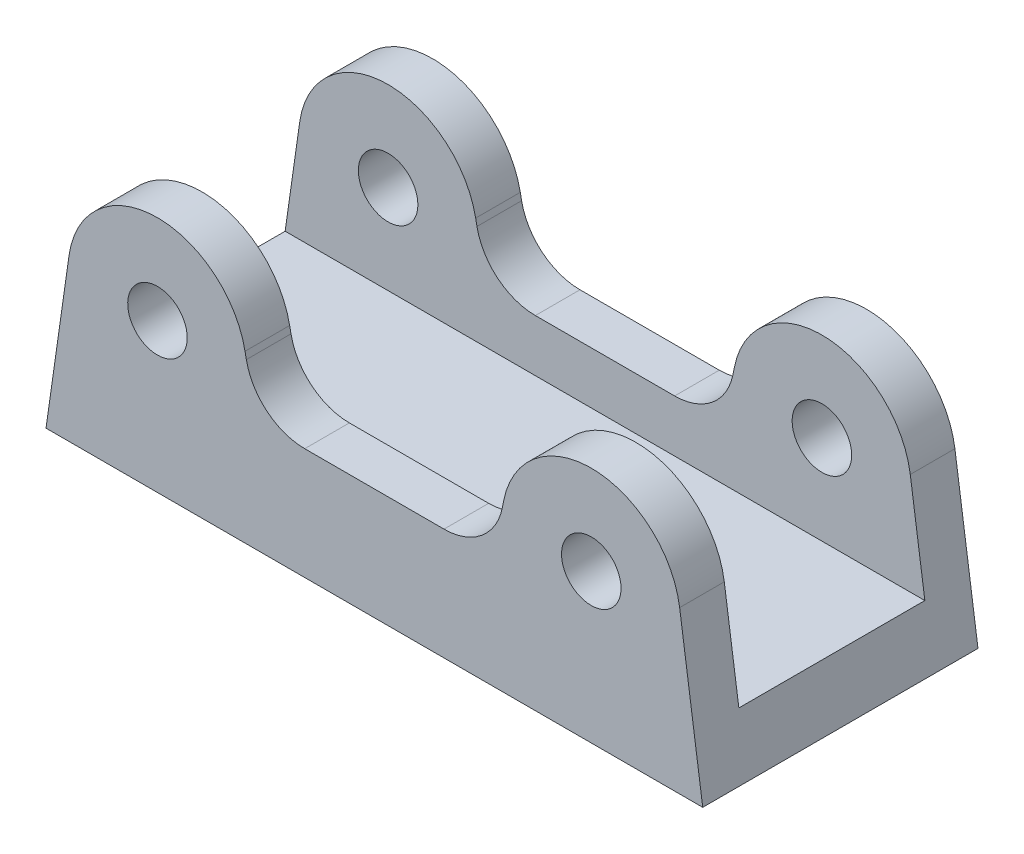
SolidWorks part; units mm, degrees
ref_plane "Front Plane" through (0, 0, 0) normal (0, 0, 1) x (1, 0, 0)
ref_plane "Top Plane" through (0, 0, 0) normal (0, 1, 0) x (1, 0, 0)
ref_plane "Right Plane" through (0, 0, 0) normal (1, 0, 0) x (0, 0, -1)
sketch "Sketch1" plane through (0, 0, 0) normal (0, 0, 1) x (1, 0, 0)
  line L0 (-29.155, 0) -> (29.155, 0) construction
  line L1 (-41.0341, 1.699) -> (-44.1376, -20)
  line L2 (-44.1376, -20) -> (44.1376, -20)
  line L3 (0, 0) -> (0, -20) construction
  line L4 (41.0341, 1.699) -> (44.1376, -20)
  line L5 (-9.3607, -5) -> (9.3607, -5)
  line L6 (-17.3837, 2.3316) -> (-17.2082, 1.4456)
  line L7 (17.3837, 2.3316) -> (17.2082, 1.4456)
  circle A0 centre (29.155, 0) radius 4
  circle A1 centre (-29.155, 0) radius 4
  arc A2 (-17.3837, 2.3316) -> (-41.0341, 1.699) centre (-29.155, 0) ccw
  arc A3 (41.0341, 1.699) -> (17.3837, 2.3316) centre (29.155, 0) ccw
  arc A4 (9.3607, -5) -> (17.2082, 1.4456) centre (9.3607, 3) ccw
  arc A5 (-9.3607, -5) -> (-17.2082, 1.4456) centre (-9.3607, 3) cw
  point P4 (0, 0)
  point P18 (0, -5)
  point P22 (15.9315, -5)
  point P25 (-15.9315, -5)
  dimension "D2" = 8
  dimension "D3" = 24
  dimension "D4" = 8
  dimension "D1" = 58.31
  dimension "D5" = 10
  dimension "D6" = 20
extrude "Boss-Extrude1" add sketch "Sketch1" along normal mid plane 37
sketch "Sketch2" plane through (0, 0, 0) normal (1, 0, 0) x (0, 0, -1)
  line L0 (-12.5, 0) -> (12.5, 0) construction
  line L1 (-12.5, 14.497) -> (12.5, 14.497)
  line L2 (-12.5, 14.497) -> (-12.5, -12)
  line L3 (-12.5, -12) -> (12.5, -12)
  line L4 (12.5, 14.497) -> (12.5, -12)
  point P8 (0, 0)
  dimension "D1" = 12
  dimension "D2" = 25
extrude "Cut-Extrude1" cut sketch "Sketch2" against normal mid plane 100
sketch3d "3DSketch1"
  line L0 (-29.155, 0, 18.5) -> (-29.155, 0, -18.5) construction
  line L1 (-29.155, 0, 18.5) -> (-29.155, 0, 12.5) construction
  line L2 (-29.155, 0, -12.5) -> (-29.155, 0, -18.5) construction
  line L3 (29.155, 0, -18.5) -> (29.155, 0, 18.5) construction
  line L4 (29.155, 0, -12.5) -> (29.155, 0, -18.5) construction
  line L5 (29.155, 0, 18.5) -> (29.155, 0, 12.5) construction
  line L6 (29.155, 0, 0) -> (-29.155, 0, 0) construction
  point P14 (0, 0, 0)
